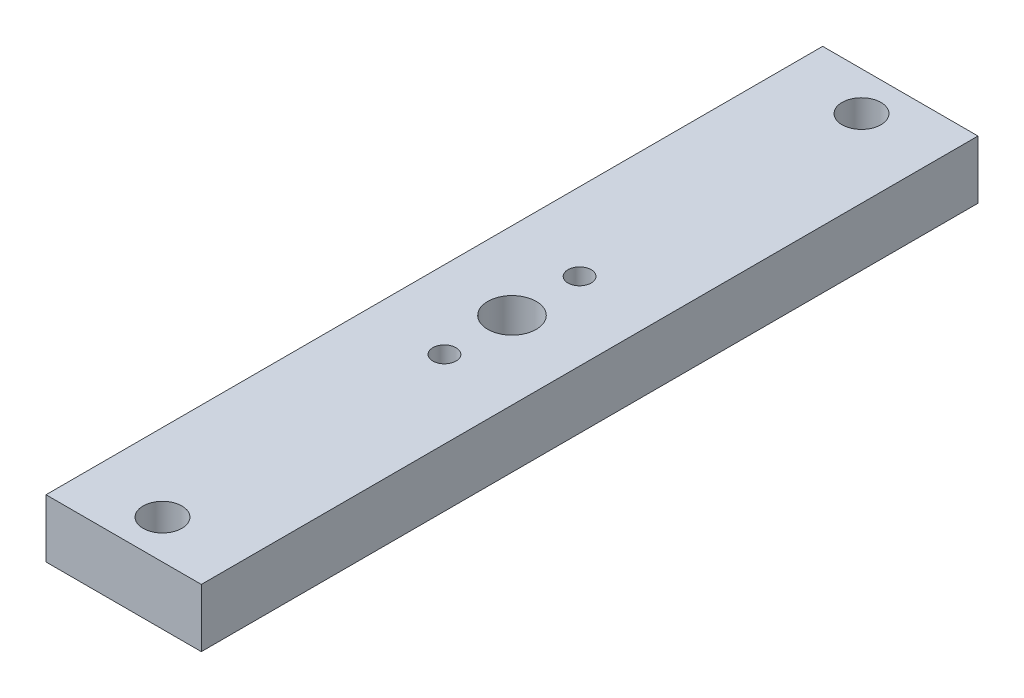
SolidWorks part; units mm, degrees
ref_plane "Front Plane" through (0, 0, 0) normal (0, 0, 1) x (1, 0, 0)
ref_plane "Top Plane" through (0, 0, 0) normal (0, 1, 0) x (1, 0, 0)
ref_plane "Right Plane" through (0, 0, 0) normal (1, 0, 0) x (0, 0, -1)
sketch "Sketch1" plane through (0, 0, 0) normal (0, 0, 1) x (1, 0, 0)
  line L0 (-12.7, -4.7625) -> (12.7, -4.7625)
  line L1 (-12.7, -4.7625) -> (-12.7, 4.7625)
  line L2 (12.7, -4.7625) -> (12.7, 4.7625)
  line L3 (-12.7, 4.7625) -> (12.7, 4.7625)
  line L4 (-12.7, -4.7625) -> (12.7, 4.7625) construction
  line L5 (12.7, -4.7625) -> (-12.7, 4.7625) construction
  point P1 (0, 0)
extrude "Extrude1" add sketch "Sketch1" along normal blind 127
sketch "Sketch2" plane through (0, 4.7625, 0) normal (0, 1, 0) x (1, 0, 0)
  line L0 (0, 0) -> (0, -6.35) construction
  line L1 (0, -127) -> (0, -120.65) construction
  line L2 (12.7, -127) -> (-12.7, -127) construction
  line L3 (-12.7, -63.5) -> (12.7, -63.5) construction
  line L4 (-12.7, -127) -> (-12.7, 0) construction
  line L5 (12.7, -127) -> (12.7, 0) construction
  line L6 (0, -63.5) -> (0, -74.549) construction
  point P13 (0, -63.5)
hole_wizard "1/4 (0.25) Diameter Hole1" positions "3DSketch1" profile "Sketch3" hole size "1/4" standard "Ansi Inch"
sketch3d "3DSketch1"
  point P0 (0, 4.7625, 6.35)
  point P4 (0, 4.7625, 120.65)
sketch "Sketch3" plane through (0, 4.7625, 6.35) normal (1, 0, 0) x (0, 0, 1)
  line L0 (0, 0) -> (0, 14.6077)
  line L1 (0, 14.6077) -> (3.175, 12.7)
  line L2 (3.175, 12.7) -> (3.175, 0)
  line L5 (3.175, 0) -> (0, 0)
  line L10 (0, 14.6077) -> (-3.175, 12.7) construction
  line L11 (0, -6.35) -> (0, 107.95) construction
  dimension "Hole Dia." = 6.35
  dimension "Hole Depth" = 12.7
  dimension "Drill Angle" = 118
hole_wizard "5/16 (0.3125) Diameter Hole1" positions "3DSketch3" profile "Sketch5" hole size "5/16" standard "Ansi Inch"
sketch3d "3DSketch3"
  point P0 (0, 4.7625, 63.5)
sketch "Sketch5" plane through (0, 4.7625, 63.5) normal (1, 0, 0) x (0, 0, 1)
  line L0 (0, 0) -> (0, 15.0847)
  line L1 (0, 15.0847) -> (3.9687, 12.7)
  line L2 (3.9687, 12.7) -> (3.9687, 0)
  line L5 (3.9687, 0) -> (0, 0)
  line L10 (0, 15.0847) -> (-3.9688, 12.7) construction
  line L11 (0, -6.35) -> (0, 107.95) construction
  dimension "Hole Dia." = 7.9375
  dimension "Hole Depth" = 12.7
  dimension "Drill Angle" = 118
hole_wizard "#25 (0.1495) Diameter Hole1" positions "3DSketch4" profile "Sketch6" hole size "#25" standard "Ansi Inch"
sketch3d "3DSketch4"
  point P0 (0, 4.7625, 74.549)
sketch "Sketch6" plane through (0, 4.7625, 74.549) normal (1, 0, 0) x (0, 0, 1)
  line L0 (0, 0) -> (0, 13.8408)
  line L1 (0, 13.8408) -> (1.8986, 12.7)
  line L2 (1.8986, 12.7) -> (1.8986, 0)
  line L5 (1.8986, 0) -> (0, 0)
  line L10 (0, 13.8408) -> (-1.8987, 12.7) construction
  line L11 (0, -6.35) -> (0, 107.95) construction
  dimension "Hole Dia." = 3.7973
  dimension "Hole Depth" = 12.7
  dimension "Drill Angle" = 118
pattern_circular "CirPattern1" count 2 over 360 about axis through (0, 0, 63.5) along (0, 1, 0) of "#25 (0.1495) Diameter Hole1"
